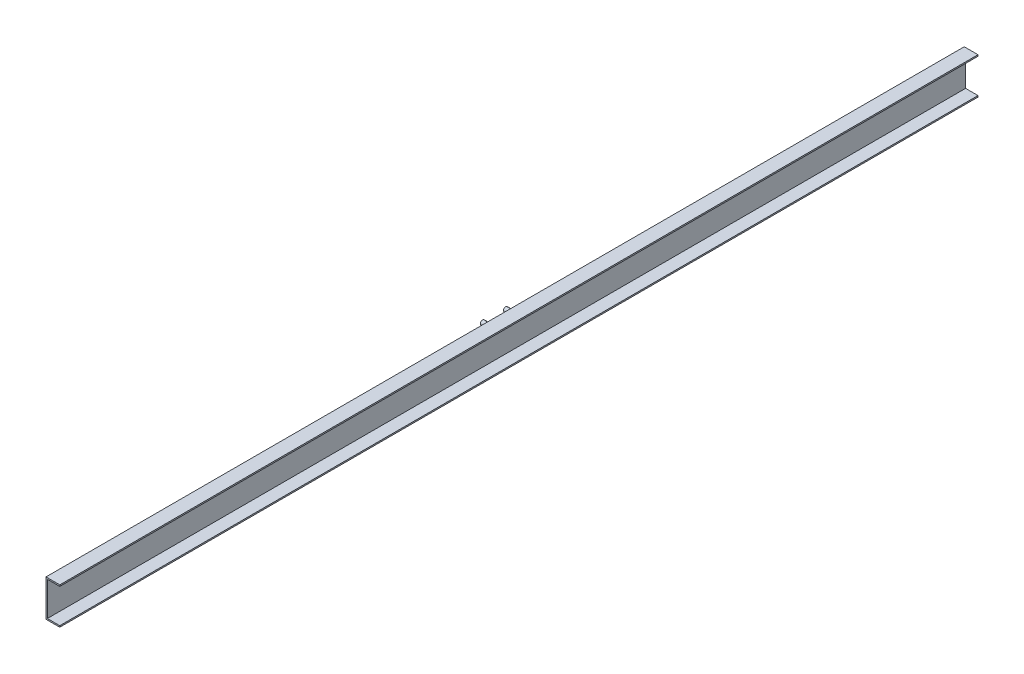
SolidWorks part; units mm, degrees
ref_plane "Alzado" through (0, 0, 0) normal (0, 0, 1) x (1, 0, 0)
ref_plane "Planta" through (0, 0, 0) normal (0, 1, 0) x (1, 0, 0)
ref_plane "Vista lateral" through (0, 0, 0) normal (1, 0, 0) x (0, 0, -1)
sketch "Croquis1" plane through (0, 0, 0) normal (0, 0, 1) x (1, 0, 0)
  line L0 (0, 0) -> (0, 80)
  line L1 (0, 80) -> (30, 80)
  line L2 (0, 0) -> (30, 0)
  line L3 (3, 3) -> (30, 3)
  line L4 (3, 3) -> (3, 77)
  line L5 (3, 77) -> (30, 77)
  line L6 (30, 77) -> (30, 80)
  line L7 (30, 3) -> (30, 0)
  dimension "D1" = 80
  dimension "D2" = 30
  dimension "D3" = 30
  dimension "D4" = 3
extrude "Saliente-Extruir1" add sketch "Croquis1" along normal blind 3500
sketch "Croquis2" plane through (0, 0, 0) normal (1, 0, 0) x (0, 0, -1)
  line L0 (-1750, 0) -> (-1750, 80) construction
  line L1 (-3500, 0) -> (0, 0) construction
  line L2 (-3500, 80) -> (0, 80) construction
  line L3 (-1750, 80) -> (-1750, 40.3027) construction
  line L4 (-1775, 40.3027) -> (-1725, 40.3027) construction
  line L5 (-1725, 40.3027) -> (-1725, 0) construction
  line L6 (-1725, 0) -> (-1725, 20.1513) construction
  line L7 (-1725, 20.1513) -> (-1663.3474, 20.1513) construction
  circle A0 centre (-1725, 20.1513) radius 4.859
  circle A1 centre (-1725, 60.454) radius 4.859
  circle A2 centre (-1775, 20.1513) radius 4.859
  circle A3 centre (-1775, 60.454) radius 4.859
  point P9 (-1850, 60.454)
  dimension "D1" = 25
extrude "Saliente-Extruir2" add sketch "Croquis2" against normal blind 24
sketch "Croquis3" plane through (0, 0, 0) normal (0, 0, 1) x (1, 0, 0)
  line L0 (37.4427, 88.0938) -> (-24.3022, 88.0938)
  line L1 (-24.3022, 88.0938) -> (-24.3022, -15.6544)
  line L2 (-24.3022, -15.6544) -> (37.4427, -15.6544)
  line L3 (37.4427, -15.6544) -> (37.4427, 88.0938)
extrude "Cortar-Extruir1" cut sketch "Croquis3" along normal blind 750
ref_plane "Plano1" through (0, 0, 3500) normal (0, 0, 1) x (1, 0, 0)
sketch "Croquis4" plane through (0, 0, 3500) normal (0, 0, 1) x (1, 0, 0)
  line L0 (34.8138, 84.0489) -> (34.8138, -6.0576)
  line L1 (34.8138, -6.0576) -> (-6.9394, -6.0576)
  line L2 (-6.9394, -6.0576) -> (-6.9394, 84.0489)
  line L3 (-6.9394, 84.0489) -> (34.8138, 84.0489)
extrude "Cortar-Extruir2" cut sketch "Croquis4" against normal blind 750
